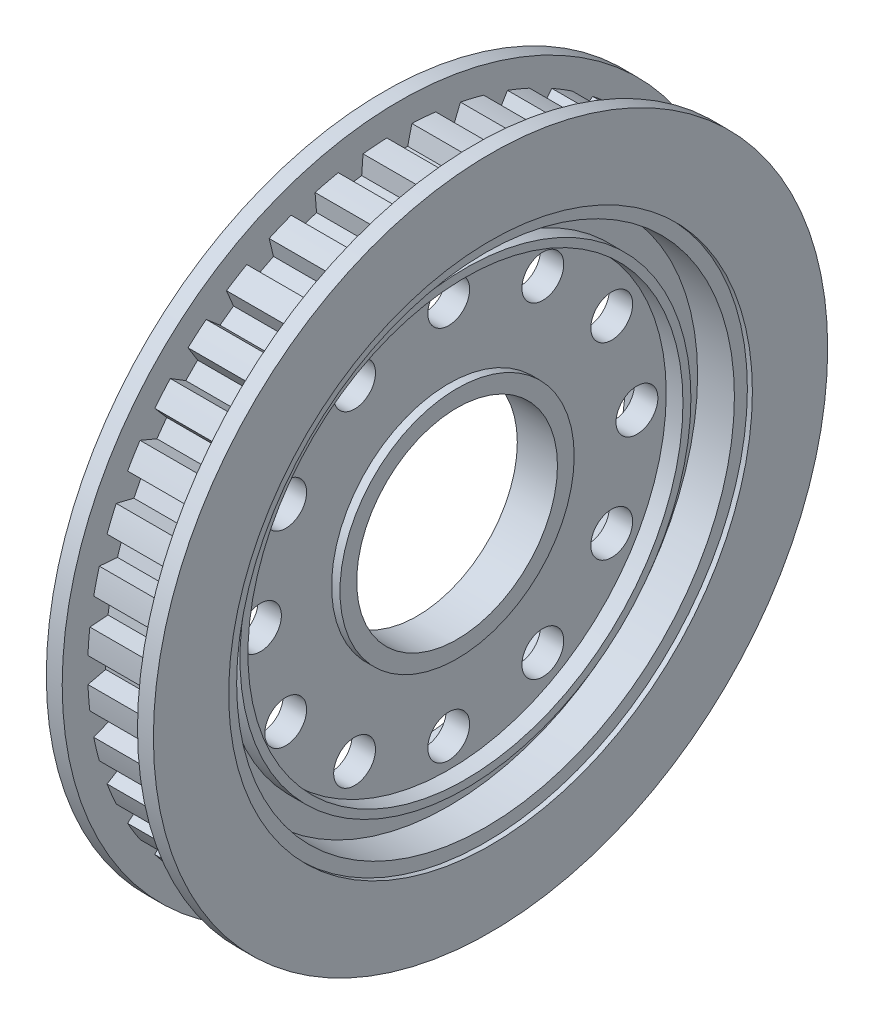
SolidWorks part; units mm, degrees
material "PVC hart"
ref_plane "Ebene vorne" through (0, 0, 0) normal (0, 0, 1) x (1, 0, 0)
ref_plane "Ebene oben" through (0, 0, 0) normal (0, 1, 0) x (1, 0, 0)
ref_plane "Ebene rechts" through (0, 0, 0) normal (1, 0, 0) x (0, 0, -1)
sketch "Skizze1" plane through (0, 0, 0) normal (0, 0, 1) x (1, 0, 0)
  line L0 (-3.7535, 0) -> (-41.8006, 0) construction
  line L1 (-3.2, 20.15) -> (-3.2, 15.65)
  line L2 (-3.2, 15.65) -> (-2.9, 15.65)
  line L3 (-2.9, 15.65) -> (-2.9, 14.875)
  line L4 (-0.7, 13.475) -> (-1.7, 13.475)
  line L5 (-1.7, 13.475) -> (-1.7, 13)
  line L6 (-1.7, 13) -> (-0.7, 13)
  line L7 (-0.7, 13) -> (-0.7, 7)
  line L8 (-0.7, 7) -> (-1.2, 7)
  line L9 (-1.2, 7) -> (-1.2, 6)
  line L10 (-1.2, 6) -> (0, 6)
  line L11 (0, 6) -> (0, 18.625)
  line L12 (0, 18.625) -> (-2.25, 18.625)
  line L13 (-2.25, 18.625) -> (-2.25, 20.15)
  line L14 (-2.25, 20.15) -> (-3.2, 20.15)
  line L15 (0, 0) -> (0, 6) construction
  line L16 (-2.9, 14.875) -> (-0.7, 14.875)
  line L17 (-0.7, 14.875) -> (-0.7, 13.475)
  dimension "D1" = 12
  dimension "D2" = 14
  dimension "D3" = 2.4
  dimension "D4" = 6.4
  dimension "D5" = 4.5
  dimension "D6" = 31.3
  dimension "D7" = 29.75
  dimension "D8" = 26
  dimension "D9" = 40.3
  dimension "D10" = 0.3
  dimension "D11" = 1.5
  dimension "D12" = 2.5
  dimension "D13" = 26.95
  dimension "D14" = 37.25
revolve "Rotation1" add sketch "Skizze1" angle 360 about L0
mirror "Spiegeln1" about plane through (0, 0, 0) normal (1, 0, 0) of bodies 101
sketch "Skizze2" plane through (-0.7, 0, 0) normal (-1, 0, 0) x (0, 0, 1)
  line L0 (0, 11.25) -> (0, 0) construction
  circle A0 centre (-5.625, 9.7428) radius 1.25
  circle A1 centre (0, 11.25) radius 1.25
  circle A2 centre (5.625, 9.7428) radius 1.25
  circle A3 centre (9.7428, 5.625) radius 1.25
  circle A4 centre (11.25, 0) radius 1.25
  circle A5 centre (9.7428, -5.625) radius 1.25
  circle A6 centre (5.625, -9.7428) radius 1.25
  circle A7 centre (0, -11.25) radius 1.25
  circle A8 centre (-5.625, -9.7428) radius 1.25
  circle A9 centre (-9.7428, -5.625) radius 1.25
  circle A10 centre (-11.25, 0) radius 1.25
  circle A11 centre (-9.7428, 5.625) radius 1.25
  point P2 (0, 0)
  point P29 (0, 0)
  dimension "D2" = 2.5
  dimension "D3" = 11.25
  dimension "D1" = 12
extrude "Schnitt-Linear austragen1" cut sketch "Skizze2" against normal through all
sketch "Skizze3" plane through (0, 0, 0) normal (1, 0, 0) x (0, 0, -1)
  line L0 (0.75, 18.6099) -> (0.5, 17.55)
  line L1 (0.5, 17.55) -> (-0.5, 17.55)
  line L2 (-0.5, 17.55) -> (-0.75, 18.6099)
  line L3 (0, 0) -> (0, 17.55) construction
  line L4 (0, 18.625) -> (0, 17.55) construction
  line L5 (0, 18.625) -> (0, 20.15) construction
  circle A0 centre (0, 0) radius 18.625 construction
  arc A1 (0.75, 18.6099) -> (-0.75, 18.6099) centre (0, 0) ccw
  circle A3 centre (0, 0) radius 20.15 construction
  dimension "D1" = 1.5
  dimension "D2" = 2.6
  dimension "D3" = 1
extrude "Schnitt-Linear austragen2" cut sketch "Skizze3" against normal mid plane 4.5
pattern_circular "Kreismuster1" count 40 over 360 about axis through (0, 0, 0) along (1, 0, 0) of "Schnitt-Linear austragen2"
